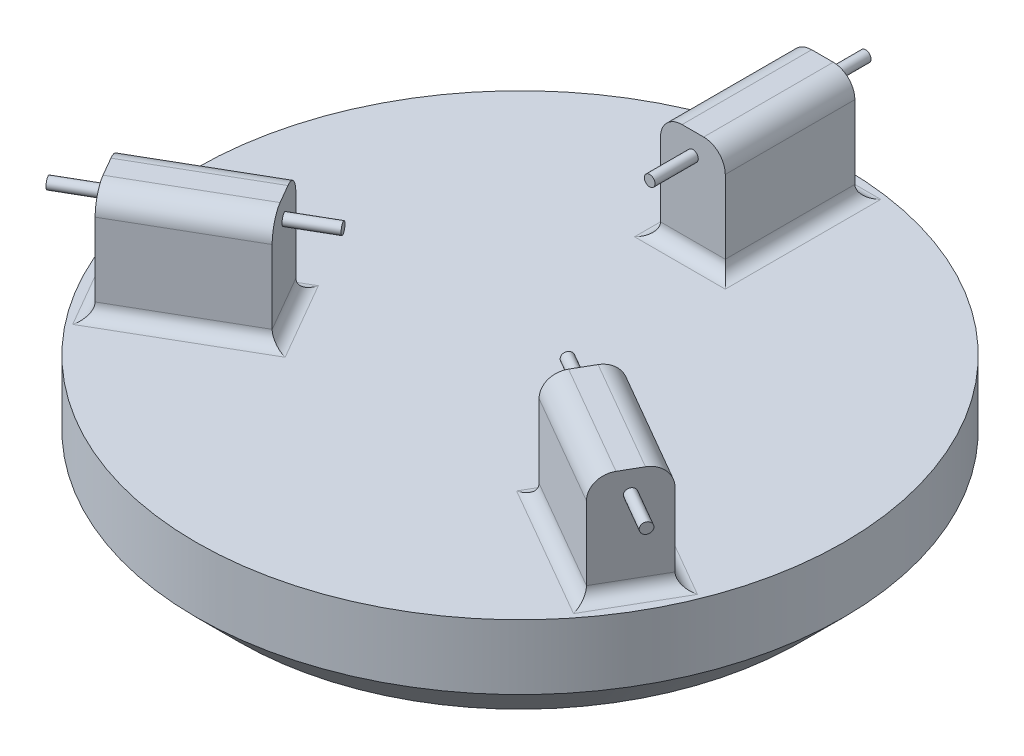
SolidWorks part; units mm, degrees
ref_plane "Front Plane" through (0, 0, 0) normal (0, 0, 1) x (1, 0, 0)
ref_plane "Top Plane" through (0, 0, 0) normal (0, 1, 0) x (1, 0, 0)
ref_plane "Right Plane" through (0, 0, 0) normal (1, 0, 0) x (0, 0, -1)
sketch "Sketch1" plane through (0, 0, 0) normal (0, 1, 0) x (1, 0, 0)
  circle A0 centre (0, 0) radius 75
  dimension "D1" = 150
extrude "Boss-Extrude1" add sketch "Sketch1" along normal blind 25
sketch "Sketch2" plane through (0, 25, 0) normal (0, 1, 0) x (1, 0, 0)
  line L0 (-64.9519, -37.5) -> (32.476, 18.75) construction
  line L1 (0, 75) -> (0, -37.5) construction
  line L2 (0, 75) -> (-64.9519, -37.5) construction
  line L3 (0, 75) -> (64.9519, -37.5) construction
  line L4 (-64.9519, -37.5) -> (64.9519, -37.5) construction
  line L5 (64.9519, -37.5) -> (-32.476, 18.75) construction
  line L6 (-64.3718, -28.5048) -> (-56.8718, -41.4952)
  line L7 (-64.3718, -28.5048) -> (-38.391, -13.5048)
  line L8 (-56.8718, -41.4952) -> (-30.891, -26.4952)
  line L9 (-38.391, -13.5048) -> (-30.891, -26.4952)
  line L10 (-7.5, 70) -> (7.5, 70)
  line L11 (7.5, 70) -> (7.5, 40)
  line L12 (-7.5, 40) -> (7.5, 40)
  line L13 (-7.5, 70) -> (-7.5, 40)
  line L14 (64.3718, -28.5048) -> (56.8718, -41.4952)
  line L15 (64.3718, -28.5048) -> (38.391, -13.5048)
  line L16 (38.391, -13.5048) -> (30.891, -26.4952)
  line L17 (56.8718, -41.4952) -> (30.891, -26.4952)
  circle A0 centre (0, 0) radius 75 construction
  point P0 (-60.6218, -35)
  dimension "D1" = 60
  dimension "D2" = 60
  dimension "D3" = 60
  dimension "D4" = 129.9038
  dimension "D5" = 5
  dimension "D6" = 30
  dimension "D7" = 15
extrude "Boss-Extrude2" add sketch "Sketch2" along normal blind 25
fillet "Fillet1" radius 3 12 edges at (60.6218, 25, 35) (51.3814, 25, 21.0048) (34.641, 25, 20) (43.8814, 25, 33.9952) (-7.5, 25, -55) (0, 25, -40) (7.5, 25, -55) (0, 25, -70) (-51.3814, 25, 21.0048) (-34.641, 25, 20) (-60.6218, 25, 35) (-43.8814, 25, 33.9952)
fillet "Fillet2" radius 5 6 edges at (43.8814, 50, 33.9952) (51.3814, 50, 21.0048) (7.5, 50, -55) (-7.5, 50, -55) (-51.3814, 50, 21.0048) (-43.8814, 50, 33.9952)
sketch "Sketch3" plane through (60.6218, 0, 35) normal (0.866, 0, 0.5) x (0.5, 0, -0.866)
  line L0 (0, 28) -> (0, 50) construction
  line L1 (-7.5, 28) -> (7.5, 28) construction
  line L2 (-2.5, 50) -> (2.5, 50) construction
  line L3 (7.5, 45) -> (7.5, 28) construction
  line L4 (-7.5, 45) -> (7.5, 45) construction
  circle A0 centre (0, 45) radius 1.25
  dimension "D1" = 2.5
extrude "Boss-Extrude3" add sketch "Sketch3" along normal blind 10
sketch "Sketch4" plane through (34.641, 0, 20) normal (-0.866, 0, -0.5) x (-0.5, 0, 0.866)
  line L0 (0, 28) -> (0, 50) construction
  line L1 (-7.5, 28) -> (7.5, 28) construction
  line L2 (-2.5, 50) -> (2.5, 50) construction
  line L3 (-7.5, 45) -> (7.5, 45) construction
  circle A0 centre (0, 45) radius 1.25
  dimension "D1" = 2.5
extrude "Boss-Extrude4" add sketch "Sketch4" along normal blind 10
sketch "Sketch5" plane through (0, 0, -70) normal (0, 0, -1) x (-1, 0, 0)
  line L0 (0, 28) -> (0, 50) construction
  line L1 (-7.5, 28) -> (7.5, 28) construction
  line L2 (-2.5, 50) -> (2.5, 50) construction
  line L3 (-7.5, 45) -> (7.5, 45) construction
  circle A0 centre (0, 45) radius 1.25
  dimension "D1" = 2.5
extrude "Boss-Extrude5" add sketch "Sketch5" along normal blind 10
sketch "Sketch6" plane through (0, 0, -40) normal (0, 0, 1) x (1, 0, 0)
  line L0 (0, 50) -> (0, 28) construction
  line L1 (-2.5, 50) -> (2.5, 50) construction
  line L2 (-7.5, 28) -> (7.5, 28) construction
  line L3 (-7.5, 45) -> (7.5, 45) construction
  circle A0 centre (0, 45) radius 1.25
  dimension "D1" = 2.5
extrude "Boss-Extrude6" add sketch "Sketch6" along normal blind 10
sketch "Sketch7" plane through (-60.6218, 0, 35) normal (-0.866, 0, 0.5) x (0.5, 0, 0.866)
  line L0 (0, 50) -> (0, 28) construction
  line L1 (-2.5, 50) -> (2.5, 50) construction
  line L2 (-7.5, 28) -> (7.5, 28) construction
  line L3 (-7.5, 45) -> (7.5, 45) construction
  circle A0 centre (0, 45) radius 1.25
  dimension "D1" = 2.5
extrude "Boss-Extrude7" add sketch "Sketch7" along normal blind 10
sketch "Sketch8" plane through (-34.641, 0, 20) normal (0.866, 0, -0.5) x (-0.5, 0, -0.866)
  line L0 (0, 50) -> (0, 28) construction
  line L1 (-2.5, 50) -> (2.5, 50) construction
  line L2 (-7.5, 28) -> (7.5, 28) construction
  line L3 (-7.5, 45) -> (7.5, 45) construction
  circle A0 centre (0, 45) radius 1.25
  dimension "D1" = 2.5
extrude "Boss-Extrude8" add sketch "Sketch8" along normal blind 10
chamfer "Chamfer1" distance 10 angle 45 1 edges at (0, 0, 75)
